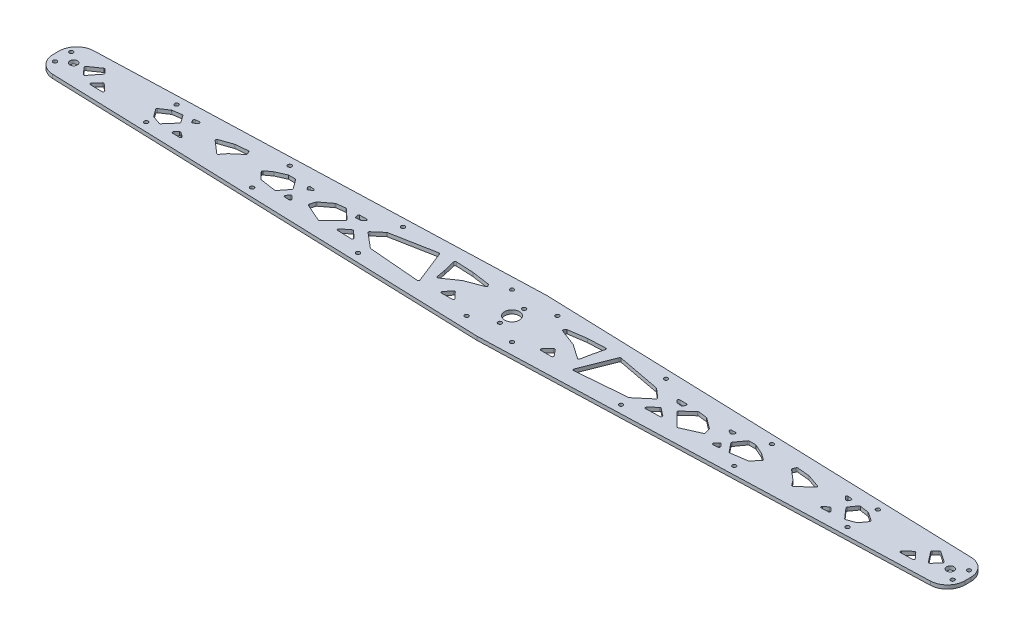
SolidWorks part; units mm, degrees
material "6061-T6 (SS)"
ref_plane "Front Plane" through (0, 0, 0) normal (0, 0, 1) x (1, 0, 0)
ref_plane "Top Plane" through (0, 0, 0) normal (0, 1, 0) x (1, 0, 0)
ref_plane "Right Plane" through (0, 0, 0) normal (1, 0, 0) x (0, 0, -1)
sketch "Sketch2" plane through (0, 0, 0) normal (0, 1, 0) x (1, 0, 0)
  line L0 (0, 0) -> (0, 30) construction
  line L1 (0, 0) -> (0, -30) construction
  line L2 (0, 0) -> (-375, 0) construction
  line L3 (-375, 17.5) -> (0, 30)
  line L4 (-375, -17.5) -> (0, -30)
  line L5 (375, -17.5) -> (0, -30)
  line L6 (375, 17.5) -> (0, 30)
  line L7 (-375, 17.5) -> (-375.4997, 17.4833)
  line L8 (-390, 2.4917) -> (-390, -2.4917)
  line L9 (-375.4997, -17.4833) -> (-375, -17.5)
  line L10 (-375, 17.5) -> (-375, -17.5) construction
  line L11 (390, 2.4917) -> (390, -2.4917)
  line L12 (375.4997, -17.4833) -> (375, -17.5)
  line L13 (375, 17.5) -> (375, -17.5) construction
  line L14 (375, 17.5) -> (375.4997, 17.4833)
  arc A2 (390, -2.4917) -> (375.4997, -17.4833) centre (375, -2.4917) cw
  arc A3 (390, 2.4917) -> (375.4997, 17.4833) centre (375, 2.4917) ccw
  arc A4 (-390, -2.4917) -> (-375.4997, -17.4833) centre (-375, -2.4917) ccw
  arc A5 (-375.4997, 17.4833) -> (-390, 2.4917) centre (-375, 2.4917) ccw
  point P15 (390, -17)
  point P18 (390, 17)
  point P21 (-390, -17)
  point P24 (-390, 17)
  point P26 (-390, 0)
  point P27 (390, 0)
  point P28 (375, 0)
  dimension "D4" = 15
  dimension "D1" = 60
  dimension "Half of Chassis Width" = 375
  dimension "FullLength" = 390
  dimension "D2" = 35
extrude "Boss-Extrude1" add sketch "Sketch2" along normal blind 3.18
sketch "Sketch3" plane through (0, 3.18, 0) normal (0, 1, 0) x (1, 0, 0)
  line L0 (0, 30) -> (0, -30) construction
  line L1 (-375, 0) -> (0, 0) construction
  line L2 (-390, 0) -> (-375, 0) construction
  line L3 (-206.25, 16.125) -> (-206.25, 0) construction
  line L4 (-112.5, -19.25) -> (-112.5, 0) construction
  line L5 (-390, 2.4917) -> (-390, -2.4917) construction
  line L6 (-375.4997, -17.4833) -> (0, -30) construction
  line L7 (-206.25, 16.125) -> (-206.25, 23.125) construction
  line L8 (0, 30) -> (-375.4997, 17.4833) construction
  line L9 (-112.5, -19.25) -> (-112.5, -26.25) construction
  line L10 (-375, 0) -> (-375, 17.5) construction
  line L11 (0, 30) -> (-375.4997, 17.4833) construction
  line L12 (-19.4207, 0) -> (-19.4207, 19.4207) construction
  line L13 (-19.4207, 19.4207) -> (0, 19.4207) construction
  line L14 (-300, 13) -> (-300, 0) construction
  line L15 (-300, 13) -> (-300, 20) construction
  line L16 (-19.4207, 19.4207) -> (-18.254, 18.254) construction
  line L17 (-18.254, 18.254) -> (-16.8397, 16.8397) construction
  line L18 (-16.8397, 16.8397) -> (0, 0) construction
  circle A0 centre (0, 0) radius 6.35
  circle A1 centre (-375, 0) radius 3.175
  circle A3 centre (-206.25, 16.125) radius 1.65
  circle A4 centre (-112.5, -19.25) radius 1.65
  circle A8 centre (375, 0) radius 3.175
  circle A9 centre (-112.5, 19.25) radius 1.65
  circle A10 centre (-206.25, -16.125) radius 1.65
  circle A11 centre (112.5, -19.25) radius 1.65
  circle A12 centre (112.5, 19.25) radius 1.65
  circle A13 centre (206.25, -16.125) radius 1.65
  circle A14 centre (206.25, 16.125) radius 1.65
  circle A15 centre (-384, 7) radius 1.65
  circle A16 centre (-384, -7) radius 1.65
  circle A17 centre (384, -7) radius 1.65
  circle A18 centre (384, 7) radius 1.65
  circle A19 centre (-19.4207, 19.4207) radius 1.65
  circle A20 centre (-19.4207, -19.4207) radius 1.65
  circle A21 centre (19.4207, -19.4207) radius 1.65
  circle A22 centre (19.4207, 19.4207) radius 1.65
  circle A23 centre (-300, 13) radius 1.65
  circle A25 centre (-300, -13) radius 1.65
  circle A26 centre (300, -13) radius 1.65
  circle A27 centre (300, 13) radius 1.65
  circle A28 centre (0, 0) radius 23.815 construction
  dimension "D1" = 12.7
  dimension "D2" = 6.35
  dimension "D3" = 3.3
  dimension "D11" = 47.63
  dimension "Hole2" = 206.25
  dimension "Hole1" = 112.5
  dimension "D5" = 7
  dimension "D6" = 7
  dimension "BallJointHoles" = 375
  dimension "D4" = 9
  dimension "D7" = 7
  dimension "D10" = 7
  dimension "Hole3" = 300
  dimension "D8" = 45
  dimension "D9" = 2
extrude "Cut-Extrude1" cut sketch "Sketch3" against normal through all
sketch "Sketch11" plane through (0, 3.18, 0) normal (0, 1, 0) x (1, 0, 0)
  line L0 (-46.9557, -13.2542) -> (-37.875, -13.2542)
  line L1 (-37.1556, -11.5596) -> (-42.0676, -6.4723)
  line L2 (-43.5604, -6.533) -> (-47.7292, -11.6204)
  line L3 (-59.5368, -3.5154) -> (-47.4685, 4.8982)
  line L4 (-47.2514, 5.0128) -> (-32.9145, 10.4523)
  line L5 (-32.4489, 11.9591) -> (-33.1525, 12.9684)
  line L6 (-33.8304, 13.3863) -> (-49.02, 15.572)
  line L7 (-49.1165, 15.5811) -> (-63.9426, 16.263)
  line L8 (-64.9605, 15.0288) -> (-62.5316, 4.9966)
  line L9 (-62.5198, 4.9409) -> (-61.0924, -2.8747)
  line L10 (-65.8675, -12.8511) -> (-76.8188, 14.811)
  line L11 (-77.9343, 15.4255) -> (-114.9795, 8.4218)
  line L12 (-115.4464, 8.1969) -> (-123.167, 1.5465)
  line L13 (-123.1594, 0.0246) -> (-110.8626, -10.3558)
  line L14 (-110.3008, -10.5882) -> (-66.8805, -14.2157)
  line L15 (-138.5004, -9.5121) -> (-132.2056, -4.6096)
  line L16 (-130.9112, -4.6653) -> (-125.244, -9.9207)
  line L17 (-125.9535, -11.6535) -> (-137.9154, -11.3006)
  line L18 (-139.7398, 9.4667) -> (-133.9309, 9.5926)
  line L19 (-133.2625, 7.8301) -> (-134.9958, 6.3603)
  line L20 (-135.5199, 6.1305) -> (-138.9791, 5.703)
  line L21 (-140.0462, 6.3668) -> (-140.6626, 8.1383)
  line L22 (-141.8691, 0.7038) -> (-150.2933, 8.5613)
  line L23 (-151.1009, 8.8221) -> (-158.4619, 7.8903)
  line L24 (-158.9389, 7.6963) -> (-167.8356, 0.9782)
  line L25 (-168.1907, 0.4679) -> (-169.5321, -3.9958)
  line L26 (-168.9782, -5.1984) -> (-153.8251, -11.8864)
  line L27 (-152.7118, -11.6762) -> (-141.8417, -0.7321)
  line L28 (-182.755, -5.2991) -> (-180.5794, -7.8233)
  line L29 (-181.4108, -9.4734) -> (-185.4398, -9.1746)
  line L30 (-186.1343, -7.5374) -> (-184.2809, -5.312)
  line L31 (-180.4874, 6.1292) -> (-178.3441, 7.4076)
  line L32 (-181.8711, 6.4975) -> (-182.6505, 7.8822)
  line L33 (-181.7428, 9.3721) -> (-178.82, 9.2658)
  line L34 (-193.789, -8.0414) -> (-187.8521, -0.5946)
  line L35 (-187.8243, 0.6157) -> (-193.4347, 8.3562)
  line L36 (-194.2443, 8.7693) -> (-199.7029, 8.7693)
  line L37 (-200.107, 8.6841) -> (-208.4203, 5.0118)
  line L38 (-208.603, 4.9067) -> (-213.9284, 1.0469)
  line L39 (-214.0726, -0.445) -> (-208.7568, -6.1417)
  line L40 (-208.1697, -6.449) -> (-194.715, -8.4076)
  line L41 (-256.6711, 4.7188) -> (-245.675, 8.5314)
  line L42 (-245.4438, 8.5819) -> (-235.1147, 9.5829)
  line L43 (-234.0978, 8.9786) -> (-233.1902, 6.8425)
  line L44 (-233.4614, 5.6908) -> (-241.6844, -1.3268)
  line L45 (-241.8289, -1.4791) -> (-245.1843, -5.8567)
  line L46 (-246.6345, -6.0026) -> (-257.0001, 3.0196)
  line L47 (-281.1371, -8.1537) -> (-278.8183, -5.8349)
  line L48 (-277.5355, -5.7243) -> (-273.9985, -8.2141)
  line L49 (-274.6033, -10.0313) -> (-280.4592, -9.8604)
  line L50 (-280.7239, 9.8026) -> (-277.4888, 10.1273)
  line L51 (-276.7474, 8.3652) -> (-279.1047, 6.3939)
  line L52 (-280.6287, 6.6905) -> (-281.5065, 8.3372)
  line L53 (-290.1682, 8.0252) -> (-297.7443, 6.8637)
  line L54 (-298.1467, 6.7077) -> (-305.2049, 2.0111)
  line L55 (-305.4627, 0.5946) -> (-301.1479, -5.4038)
  line L56 (-300.6722, -5.7617) -> (-293.6679, -8.2613)
  line L57 (-292.5783, -7.9769) -> (-285.1124, 0.5795)
  line L58 (-285.0527, 1.8189) -> (-289.2035, 7.6187)
  line L63 (-360.7214, -4.4562) -> (-353.8164, 4.2927)
  line L64 (-353.8724, 5.5968) -> (-356.7795, 8.6925)
  line L65 (-358.0768, 8.8307) -> (-367.0377, 2.6417)
  line L66 (-367.221, 1.1593) -> (-362.258, -4.4963)
  line L67 (-352.3728, -7.3942) -> (-347.9195, -2.4852)
  line L68 (-346.5069, -2.4165) -> (-340.9196, -7.4852)
  line L69 (-341.6074, -9.2257) -> (-351.6481, -9.066)
  line L70 (0, 30) -> (0, -30) construction
  line L71 (37.1556, -11.5596) -> (42.0676, -6.4723)
  line L72 (46.9557, -13.2542) -> (37.875, -13.2542)
  line L73 (43.5604, -6.533) -> (47.7292, -11.6204)
  line L74 (64.9605, 15.0288) -> (62.5316, 4.9966)
  line L75 (49.1165, 15.5811) -> (63.9426, 16.263)
  line L76 (33.8304, 13.3863) -> (49.02, 15.572)
  line L77 (32.4489, 11.9591) -> (33.1525, 12.9684)
  line L78 (47.2514, 5.0128) -> (32.9145, 10.4523)
  line L79 (59.5368, -3.5154) -> (47.4685, 4.8982)
  line L80 (62.5198, 4.9409) -> (61.0924, -2.8747)
  line L81 (123.1594, 0.0246) -> (110.8626, -10.3558)
  line L82 (115.4464, 8.1969) -> (123.167, 1.5465)
  line L83 (77.9343, 15.4255) -> (114.9795, 8.4218)
  line L84 (65.8675, -12.8511) -> (76.8188, 14.811)
  line L85 (110.3008, -10.5882) -> (66.8805, -14.2157)
  line L86 (135.5199, 6.1305) -> (138.9791, 5.703)
  line L87 (133.2625, 7.8301) -> (134.9958, 6.3603)
  line L88 (139.7398, 9.4667) -> (133.9309, 9.5926)
  line L89 (140.0462, 6.3668) -> (140.6626, 8.1383)
  line L90 (130.9112, -4.6653) -> (125.244, -9.9207)
  line L91 (138.5004, -9.5121) -> (132.2056, -4.6096)
  line L92 (125.9535, -11.6535) -> (137.9154, -11.3006)
  line L93 (168.9782, -5.1984) -> (153.8251, -11.8864)
  line L94 (168.1907, 0.4679) -> (169.5321, -3.9958)
  line L95 (158.9389, 7.6963) -> (167.8356, 0.9782)
  line L96 (151.1009, 8.8221) -> (158.4619, 7.8903)
  line L97 (141.8691, 0.7038) -> (150.2933, 8.5613)
  line L98 (152.7118, -11.6762) -> (141.8417, -0.7321)
  line L99 (181.8711, 6.4975) -> (182.6505, 7.8822)
  line L100 (180.4874, 6.1292) -> (178.3441, 7.4076)
  line L101 (181.7428, 9.3721) -> (178.82, 9.2658)
  line L102 (181.4108, -9.4734) -> (185.4398, -9.1746)
  line L103 (182.755, -5.2991) -> (180.5794, -7.8233)
  line L104 (186.1343, -7.5374) -> (184.2809, -5.312)
  line L105 (214.0726, -0.445) -> (208.7568, -6.1417)
  line L106 (208.603, 4.9067) -> (213.9284, 1.0469)
  line L107 (200.107, 8.6841) -> (208.4203, 5.0118)
  line L108 (194.2443, 8.7693) -> (199.7029, 8.7693)
  line L109 (187.8243, 0.6157) -> (193.4347, 8.3562)
  line L110 (193.789, -8.0414) -> (187.8521, -0.5946)
  line L111 (208.1697, -6.449) -> (194.715, -8.4076)
  line L112 (241.8289, -1.4791) -> (245.1843, -5.8567)
  line L113 (233.4614, 5.6908) -> (241.6844, -1.3268)
  line L114 (234.0978, 8.9786) -> (233.1902, 6.8425)
  line L115 (245.4438, 8.5819) -> (235.1147, 9.5829)
  line L116 (256.6711, 4.7188) -> (245.675, 8.5314)
  line L117 (246.6345, -6.0026) -> (257.0001, 3.0196)
  line L118 (276.7474, 8.3652) -> (279.1047, 6.3939)
  line L119 (280.7239, 9.8026) -> (277.4888, 10.1273)
  line L120 (280.6287, 6.6905) -> (281.5065, 8.3372)
  line L123 (277.5355, -5.7243) -> (273.9985, -8.2141)
  line L124 (281.1371, -8.1537) -> (278.8183, -5.8349)
  line L125 (274.6033, -10.0313) -> (280.4592, -9.8604)
  line L126 (292.5783, -7.9769) -> (285.1124, 0.5795)
  line L127 (300.6722, -5.7617) -> (293.6679, -8.2613)
  line L128 (305.4627, 0.5946) -> (301.1479, -5.4038)
  line L129 (298.1467, 6.7077) -> (305.2049, 2.0111)
  line L130 (290.1682, 8.0252) -> (297.7443, 6.8637)
  line L131 (285.0527, 1.8189) -> (289.2035, 7.6187)
  line L132 (358.0768, 8.8307) -> (367.0377, 2.6417)
  line L133 (353.8724, 5.5968) -> (356.7795, 8.6925)
  line L134 (360.7214, -4.4562) -> (353.8164, 4.2927)
  line L135 (367.221, 1.1593) -> (362.258, -4.4963)
  line L136 (346.5069, -2.4165) -> (340.9196, -7.4852)
  line L137 (352.3728, -7.3942) -> (347.9195, -2.4852)
  line L138 (341.6074, -9.2257) -> (351.6481, -9.066)
  arc A8 (-245.1843, -5.8567) -> (-246.6345, -6.0026) centre (-245.978, -5.2484) cw
  arc A9 (-241.6844, -1.3268) -> (-241.8289, -1.4791) centre (-241.0352, -2.0874) ccw
  arc A10 (-233.1902, 6.8425) -> (-233.4614, 5.6908) centre (-234.1106, 6.4514) cw
  arc A11 (-235.1147, 9.5829) -> (-234.0978, 8.9786) centre (-235.0182, 8.5876) cw
  arc A12 (-245.675, 8.5314) -> (-245.4438, 8.5819) centre (-245.3474, 7.5866) cw
  arc A13 (-256.6711, 4.7188) -> (-257.0001, 3.0196) centre (-256.3435, 3.7739) ccw
  arc A14 (-277.4888, 10.1273) -> (-276.7474, 8.3652) centre (-277.3889, 9.1323) cw
  arc A15 (-280.7239, 9.8026) -> (-281.5065, 8.3372) centre (-280.6241, 8.8076) ccw
  arc A16 (-279.1047, 6.3939) -> (-280.6287, 6.6905) centre (-279.7462, 7.161) cw
  arc A17 (-273.9985, -8.2141) -> (-274.6033, -10.0313) centre (-274.5742, -9.0318) cw
  arc A18 (-281.1371, -8.1537) -> (-280.4592, -9.8604) centre (-280.43, -8.8608) ccw
  arc A19 (-278.8183, -5.8349) -> (-277.5355, -5.7243) centre (-278.1112, -6.542) cw
  arc A20 (-301.1479, -5.4038) -> (-300.6722, -5.7617) centre (-300.3361, -4.8199) ccw
  arc A21 (-305.2049, 2.0111) -> (-305.4627, 0.5946) centre (-304.6509, 1.1785) ccw
  arc A22 (-297.7443, 6.8637) -> (-298.1467, 6.7077) centre (-297.5928, 5.8752) ccw
  arc A23 (-290.1682, 8.0252) -> (-289.2035, 7.6187) centre (-290.0167, 7.0367) cw
  arc A24 (-285.1124, 0.5795) -> (-285.0527, 1.8189) centre (-285.8659, 1.2369) ccw
  arc A25 (-293.6679, -8.2613) -> (-292.5783, -7.9769) centre (-293.3318, -7.3195) ccw
  arc A26 (-340.9196, -7.4852) -> (-341.6074, -9.2257) centre (-341.5915, -8.2258) cw
  arc A27 (-352.3728, -7.3942) -> (-351.6481, -9.066) centre (-351.6322, -8.0661) ccw
  arc A28 (-347.9195, -2.4852) -> (-346.5069, -2.4165) centre (-347.1788, -3.1571) cw
  arc A29 (-353.8164, 4.2927) -> (-353.8724, 5.5968) centre (-354.6014, 4.9123) ccw
  arc A30 (-360.7214, -4.4562) -> (-362.258, -4.4963) centre (-361.5064, -3.8367) cw
  arc A31 (-367.0377, 2.6417) -> (-367.221, 1.1593) centre (-366.4694, 1.8189) ccw
  arc A32 (-356.7795, 8.6925) -> (-358.0768, 8.8307) centre (-357.5085, 8.0079) ccw
  arc A33 (-37.875, -13.2542) -> (-37.1556, -11.5596) centre (-37.875, -12.2542) ccw
  arc A34 (-46.9557, -13.2542) -> (-47.7292, -11.6204) centre (-46.9557, -12.2542) cw
  arc A35 (-42.0676, -6.4723) -> (-43.5604, -6.533) centre (-42.787, -7.1669) ccw
  arc A36 (-32.9145, 10.4523) -> (-32.4489, 11.9591) centre (-33.2692, 11.3872) ccw
  arc A37 (-33.1525, 12.9684) -> (-33.8304, 13.3863) centre (-33.9728, 12.3965) ccw
  arc A38 (-49.02, 15.572) -> (-49.1165, 15.5811) centre (-49.1625, 14.5822) ccw
  arc A39 (-47.4685, 4.8982) -> (-47.2514, 5.0128) centre (-46.8967, 4.0778) cw
  arc A40 (-62.5316, 4.9966) -> (-62.5198, 4.9409) centre (-63.5035, 4.7613) cw
  arc A41 (-59.5368, -3.5154) -> (-61.0924, -2.8747) centre (-60.1087, -2.695) cw
  arc A42 (-63.9426, 16.263) -> (-64.9605, 15.0288) centre (-63.9885, 15.2641) ccw
  arc A43 (-76.8188, 14.811) -> (-77.9343, 15.4255) centre (-77.7486, 14.4429) ccw
  arc A44 (-65.8675, -12.8511) -> (-66.8805, -14.2157) centre (-66.7973, -13.2192) cw
  arc A45 (-110.8626, -10.3558) -> (-110.3008, -10.5882) centre (-110.2175, -9.5917) ccw
  arc A46 (-114.9795, 8.4218) -> (-115.4464, 8.1969) centre (-114.7937, 7.4393) ccw
  arc A47 (-123.167, 1.5465) -> (-123.1594, 0.0246) centre (-122.5144, 0.7888) ccw
  arc A48 (-138.5004, -9.5121) -> (-137.9154, -11.3006) centre (-137.8859, -10.301) ccw
  arc A49 (-125.244, -9.9207) -> (-125.9535, -11.6535) centre (-125.924, -10.654) cw
  arc A50 (-132.2056, -4.6096) -> (-130.9112, -4.6653) centre (-131.5912, -5.3986) cw
  arc A51 (-138.9791, 5.703) -> (-140.0462, 6.3668) centre (-139.1017, 6.6954) cw
  arc A52 (-134.9958, 6.3603) -> (-135.5199, 6.1305) centre (-135.6426, 7.123) cw
  arc A53 (-133.9309, 9.5926) -> (-133.2625, 7.8301) centre (-133.9092, 8.5928) cw
  arc A54 (-139.7398, 9.4667) -> (-140.6626, 8.1383) centre (-139.7182, 8.4669) ccw
  arc A55 (-169.5321, -3.9958) -> (-168.9782, -5.1984) centre (-168.5744, -4.2836) ccw
  arc A56 (-167.8356, 0.9782) -> (-168.1907, 0.4679) centre (-167.233, 0.1801) ccw
  arc A57 (-158.4619, 7.8903) -> (-158.9389, 7.6963) centre (-158.3363, 6.8983) ccw
  arc A58 (-150.2933, 8.5613) -> (-151.1009, 8.8221) centre (-150.9754, 7.83) ccw
  arc A59 (-141.8691, 0.7038) -> (-141.8417, -0.7321) centre (-142.5512, -0.0274) cw
  arc A60 (-153.8251, -11.8864) -> (-152.7118, -11.6762) centre (-153.4213, -10.9715) ccw
  arc A61 (-180.4874, 6.1292) -> (-181.8711, 6.4975) centre (-180.9997, 6.988) cw
  arc A62 (-182.6505, 7.8822) -> (-181.7428, 9.3721) centre (-181.7791, 8.3727) cw
  arc A63 (-178.3441, 7.4076) -> (-178.82, 9.2658) centre (-178.8564, 8.2665) ccw
  arc A64 (-185.4398, -9.1746) -> (-186.1343, -7.5374) centre (-185.3659, -8.1773) cw
  arc A65 (-180.5794, -7.8233) -> (-181.4108, -9.4734) centre (-181.3369, -8.4762) cw
  arc A66 (-182.755, -5.2991) -> (-184.2809, -5.312) centre (-183.5125, -5.9519) ccw
  arc A67 (-208.4203, 5.0118) -> (-208.603, 4.9067) centre (-208.0162, 4.097) ccw
  arc A68 (-213.9284, 1.0469) -> (-214.0726, -0.445) centre (-213.3415, 0.2372) ccw
  arc A69 (-208.7568, -6.1417) -> (-208.1697, -6.449) centre (-208.0257, -5.4594) ccw
  arc A70 (-193.789, -8.0414) -> (-194.715, -8.4076) centre (-194.571, -7.418) cw
  arc A71 (-187.8521, -0.5946) -> (-187.8243, 0.6157) centre (-188.634, 0.0288) ccw
  arc A72 (-193.4347, 8.3562) -> (-194.2443, 8.7693) centre (-194.2443, 7.7693) ccw
  arc A73 (-199.7029, 8.7693) -> (-200.107, 8.6841) centre (-199.7029, 7.7693) ccw
  arc A74 (37.875, -13.2542) -> (37.1556, -11.5596) centre (37.875, -12.2542) cw
  arc A75 (46.9557, -13.2542) -> (47.7292, -11.6204) centre (46.9557, -12.2542) ccw
  arc A76 (42.0676, -6.4723) -> (43.5604, -6.533) centre (42.787, -7.1669) cw
  arc A77 (63.9426, 16.263) -> (64.9605, 15.0288) centre (63.9885, 15.2641) cw
  arc A78 (49.02, 15.572) -> (49.1165, 15.5811) centre (49.1625, 14.5822) cw
  arc A79 (33.1525, 12.9684) -> (33.8304, 13.3863) centre (33.9728, 12.3965) cw
  arc A80 (32.9145, 10.4523) -> (32.4489, 11.9591) centre (33.2692, 11.3872) cw
  arc A81 (47.4685, 4.8982) -> (47.2514, 5.0128) centre (46.8967, 4.0778) ccw
  arc A82 (62.5316, 4.9966) -> (62.5198, 4.9409) centre (63.5035, 4.7613) ccw
  arc A83 (59.5368, -3.5154) -> (61.0924, -2.8747) centre (60.1087, -2.695) ccw
  arc A84 (123.167, 1.5465) -> (123.1594, 0.0246) centre (122.5144, 0.7888) cw
  arc A85 (114.9795, 8.4218) -> (115.4464, 8.1969) centre (114.7937, 7.4393) cw
  arc A86 (76.8188, 14.811) -> (77.9343, 15.4255) centre (77.7486, 14.4429) cw
  arc A87 (65.8675, -12.8511) -> (66.8805, -14.2157) centre (66.7973, -13.2192) ccw
  arc A88 (110.8626, -10.3558) -> (110.3008, -10.5882) centre (110.2175, -9.5917) cw
  arc A89 (134.9958, 6.3603) -> (135.5199, 6.1305) centre (135.6426, 7.123) ccw
  arc A90 (133.9309, 9.5926) -> (133.2625, 7.8301) centre (133.9092, 8.5928) ccw
  arc A91 (138.9791, 5.703) -> (140.0462, 6.3668) centre (139.1017, 6.6954) ccw
  arc A92 (139.7398, 9.4667) -> (140.6626, 8.1383) centre (139.7182, 8.4669) cw
  arc A93 (132.2056, -4.6096) -> (130.9112, -4.6653) centre (131.5912, -5.3986) ccw
  arc A94 (138.5004, -9.5121) -> (137.9154, -11.3006) centre (137.8859, -10.301) cw
  arc A95 (125.244, -9.9207) -> (125.9535, -11.6535) centre (125.924, -10.654) ccw
  arc A96 (169.5321, -3.9958) -> (168.9782, -5.1984) centre (168.5744, -4.2836) cw
  arc A97 (167.8356, 0.9782) -> (168.1907, 0.4679) centre (167.233, 0.1801) cw
  arc A98 (158.4619, 7.8903) -> (158.9389, 7.6963) centre (158.3363, 6.8983) cw
  arc A99 (150.2933, 8.5613) -> (151.1009, 8.8221) centre (150.9754, 7.83) cw
  arc A100 (141.8691, 0.7038) -> (141.8417, -0.7321) centre (142.5512, -0.0274) ccw
  arc A101 (153.8251, -11.8864) -> (152.7118, -11.6762) centre (153.4213, -10.9715) cw
  arc A102 (180.4874, 6.1292) -> (181.8711, 6.4975) centre (180.9997, 6.988) ccw
  arc A103 (182.6505, 7.8822) -> (181.7428, 9.3721) centre (181.7791, 8.3727) ccw
  arc A104 (178.3441, 7.4076) -> (178.82, 9.2658) centre (178.8564, 8.2665) cw
  arc A105 (180.5794, -7.8233) -> (181.4108, -9.4734) centre (181.3369, -8.4762) ccw
  arc A106 (185.4398, -9.1746) -> (186.1343, -7.5374) centre (185.3659, -8.1773) ccw
  arc A107 (182.755, -5.2991) -> (184.2809, -5.312) centre (183.5125, -5.9519) cw
  arc A108 (213.9284, 1.0469) -> (214.0726, -0.445) centre (213.3415, 0.2372) cw
  arc A109 (208.4203, 5.0118) -> (208.603, 4.9067) centre (208.0162, 4.097) cw
  arc A110 (199.7029, 8.7693) -> (200.107, 8.6841) centre (199.7029, 7.7693) cw
  arc A111 (193.4347, 8.3562) -> (194.2443, 8.7693) centre (194.2443, 7.7693) cw
  arc A112 (187.8521, -0.5946) -> (187.8243, 0.6157) centre (188.634, 0.0288) cw
  arc A113 (208.7568, -6.1417) -> (208.1697, -6.449) centre (208.0257, -5.4594) cw
  arc A114 (193.789, -8.0414) -> (194.715, -8.4076) centre (194.571, -7.418) ccw
  arc A115 (241.6844, -1.3268) -> (241.8289, -1.4791) centre (241.0352, -2.0874) cw
  arc A116 (233.1902, 6.8425) -> (233.4614, 5.6908) centre (234.1106, 6.4514) ccw
  arc A117 (235.1147, 9.5829) -> (234.0978, 8.9786) centre (235.0182, 8.5876) ccw
  arc A118 (245.675, 8.5314) -> (245.4438, 8.5819) centre (245.3474, 7.5866) ccw
  arc A119 (245.1843, -5.8567) -> (246.6345, -6.0026) centre (245.978, -5.2484) ccw
  arc A120 (256.6711, 4.7188) -> (257.0001, 3.0196) centre (256.3435, 3.7739) cw
  arc A121 (277.4888, 10.1273) -> (276.7474, 8.3652) centre (277.3889, 9.1323) ccw
  arc A122 (280.7239, 9.8026) -> (281.5065, 8.3372) centre (280.6241, 8.8076) cw
  arc A123 (279.1047, 6.3939) -> (280.6287, 6.6905) centre (279.7462, 7.161) ccw
  arc A130 (278.8183, -5.8349) -> (277.5355, -5.7243) centre (278.1112, -6.542) ccw
  arc A131 (273.9985, -8.2141) -> (274.6033, -10.0313) centre (274.5742, -9.0318) ccw
  arc A132 (281.1371, -8.1537) -> (280.4592, -9.8604) centre (280.43, -8.8608) cw
  arc A133 (293.6679, -8.2613) -> (292.5783, -7.9769) centre (293.3318, -7.3195) cw
  arc A134 (301.1479, -5.4038) -> (300.6722, -5.7617) centre (300.3361, -4.8199) cw
  arc A135 (305.2049, 2.0111) -> (305.4627, 0.5946) centre (304.6509, 1.1785) cw
  arc A136 (297.7443, 6.8637) -> (298.1467, 6.7077) centre (297.5928, 5.8752) cw
  arc A137 (290.1682, 8.0252) -> (289.2035, 7.6187) centre (290.0167, 7.0367) ccw
  arc A138 (285.1124, 0.5795) -> (285.0527, 1.8189) centre (285.8659, 1.2369) cw
  arc A139 (356.7795, 8.6925) -> (358.0768, 8.8307) centre (357.5085, 8.0079) cw
  arc A140 (353.8164, 4.2927) -> (353.8724, 5.5968) centre (354.6014, 4.9123) cw
  arc A141 (360.7214, -4.4562) -> (362.258, -4.4963) centre (361.5064, -3.8367) ccw
  arc A142 (367.0377, 2.6417) -> (367.221, 1.1593) centre (366.4694, 1.8189) cw
  arc A143 (347.9195, -2.4852) -> (346.5069, -2.4165) centre (347.1788, -3.1571) ccw
  arc A144 (340.9196, -7.4852) -> (341.6074, -9.2257) centre (341.5915, -8.2258) ccw
  arc A145 (352.3728, -7.3942) -> (351.6481, -9.066) centre (351.6322, -8.0661) cw
  dimension "D5" = 1
  dimension "D6" = 1
  dimension "D7" = 1
  dimension "D8" = 1
  dimension "D9" = 1
  dimension "D10" = 1
  dimension "D11" = 1
  dimension "D12" = 1
  dimension "D13" = 1
  dimension "D14" = 1
  dimension "D15" = 1
  dimension "D16" = 1
  dimension "D17" = 1
  dimension "D18" = 1
  dimension "D19" = 1
  dimension "D20" = 1
  dimension "D21" = 1
  dimension "D22" = 1
  dimension "D23" = 1
  dimension "D24" = 1
  dimension "D25" = 1
  dimension "D26" = 1
  dimension "D27" = 1
  dimension "D28" = 1
  dimension "D29" = 1
  dimension "D30" = 1
  dimension "D31" = 1
  dimension "D32" = 1
  dimension "D33" = 1
  dimension "D34" = 1
  dimension "D35" = 1
  dimension "D36" = 1
  dimension "D37" = 1
  dimension "D38" = 1
  dimension "D39" = 1
  dimension "D40" = 1
  dimension "D41" = 1
  dimension "D42" = 1
  dimension "D43" = 1
  dimension "D44" = 1
  dimension "D45" = 1
  dimension "D46" = 1
  dimension "D47" = 1
  dimension "D48" = 1
  dimension "D49" = 1
  dimension "D50" = 1
  dimension "D51" = 1
  dimension "D52" = 1
  dimension "D53" = 1
  dimension "D54" = 1
  dimension "D55" = 1
  dimension "D56" = 1
  dimension "D57" = 1
  dimension "D58" = 1
  dimension "D59" = 1
  dimension "D60" = 1
  dimension "D61" = 1
  dimension "D62" = 1
  dimension "D63" = 1
  dimension "D64" = 1
  dimension "D65" = 1
  dimension "D66" = 1
  dimension "D67" = 1
  dimension "D68" = 1
  dimension "D69" = 1
  dimension "D70" = 1
extrude "Cut-Extrude8" cut sketch "Sketch11" against normal through all
sketch "Sketch12" plane through (0, 3.18, 0) normal (0, 1, 0) x (1, 0, 0)
  line L0 (0, -10.3187) -> (0, 10.3187) construction
  circle A0 centre (0, 10.3187) radius 1.65
  circle A1 centre (0, -10.3187) radius 1.65
  point P9 (0, 0)
  dimension "D1" = 3.3
  dimension "D2" = 20.6375
extrude "Cut-Extrude9" cut sketch "Sketch12" against normal through all
equation "\"Hole2@Sketch3\"= \"Chassis Width@Differential System Assy - Option 1.Assembly\" / 2 * 0.55"
equation "\"Hole1@Sketch3\" = \"Chassis Width@Differential System Assy - Option 1.Assembly\" / 2 * 0.3"
equation "\"Half of Chassis Width@Sketch2\"= \"Chassis Width@Differential System Assy - Option 1.Assembly\" / 2"
equation "\"FullLength@Sketch2\"= \"Chassis Width@Differential System Assy - Option 1.Assembly\" / 2 * 1.04"
equation "\"BallJointHoles@Sketch3\"= \"Chassis Width@Differential System Assy - Option 1.Assembly\" / 2"
equation "\"Hole3@Sketch3\"= \"Chassis Width@Differential System Assy - Option 1.Assembly\" / 2 * 0.8"
